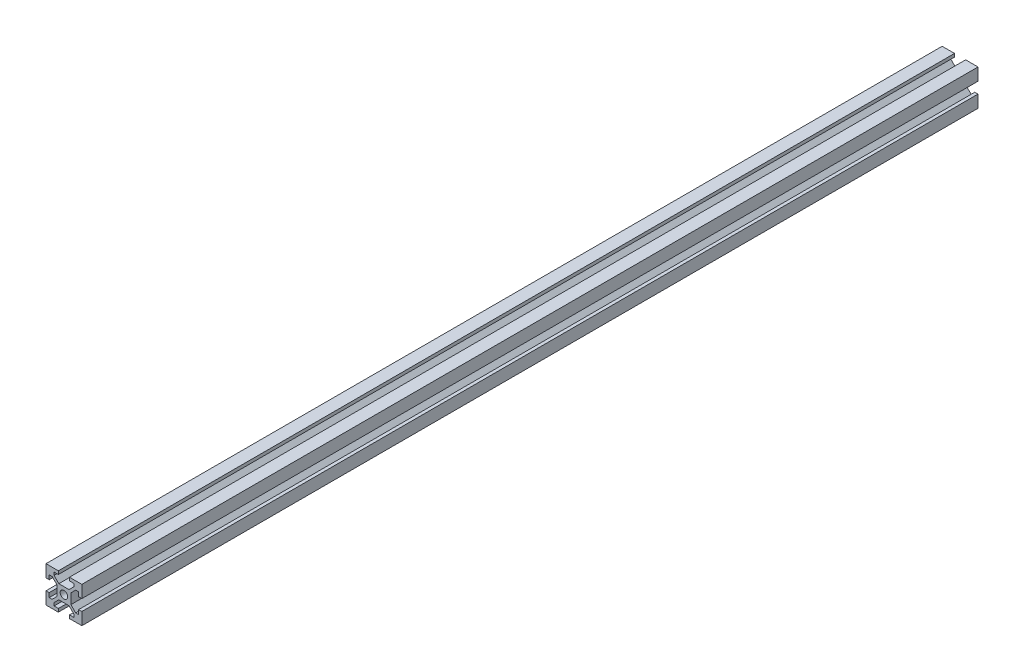
SolidWorks part; units mm, degrees
ref_plane "Front Plane" through (0, 0, 0) normal (0, 0, 1) x (1, 0, 0)
ref_plane "Top Plane" through (0, 0, 0) normal (0, 1, 0) x (1, 0, 0)
ref_plane "Right Plane" through (0, 0, 0) normal (1, 0, 0) x (0, 0, -1)
sketch "Sketch1" plane through (0, 0, 0) normal (0, 0, 1) x (1, 0, 0)
  line L0 (-3.1, 10) -> (-3.1, 8.2007)
  line L1 (-10, 10) -> (-3.1, 10)
  line L2 (-10, 10) -> (-10, 3.1)
  line L3 (-10, -10) -> (-3.1, -10)
  line L4 (10, 10) -> (10, 3.1)
  line L5 (-10, 10) -> (10, -10) construction
  line L6 (-10, -10) -> (10, 10) construction
  line L7 (-3.1, 8.2007) -> (-5.5, 8.2007)
  line L8 (-5.5, 8.2007) -> (-5.5, 6.5607)
  line L9 (-5.5, 6.5607) -> (-2.84, 3.9007)
  line L10 (-2.84, 3.9007) -> (2.84, 3.9007)
  line L11 (2.84, 3.9007) -> (5.5, 6.5607)
  line L12 (5.5, 6.5607) -> (5.5, 8.2007)
  line L13 (5.5, 8.2007) -> (3.1, 8.2007)
  line L14 (3.1, 8.2007) -> (3.1, 10)
  line L15 (-3.1, 8.2007) -> (3.1, 8.2007) construction
  line L16 (-5.5, 6.5607) -> (5.5, 6.5607) construction
  line L17 (3.1, 10) -> (10, 10)
  line L18 (8.2007, 3.1) -> (8.2007, 5.5)
  line L19 (8.2007, 5.5) -> (6.5607, 5.5)
  line L20 (6.5607, 5.5) -> (3.9007, 2.84)
  line L21 (3.9007, 2.84) -> (3.9007, -2.84)
  line L22 (3.9007, -2.84) -> (6.5607, -5.5)
  line L23 (6.5607, -5.5) -> (8.2007, -5.5)
  line L24 (8.2007, -5.5) -> (8.2007, -3.1)
  line L25 (8.2007, 3.1) -> (8.2007, -3.1) construction
  line L26 (6.5607, 5.5) -> (6.5607, -5.5) construction
  line L27 (10, 3.1) -> (8.2007, 3.1)
  line L28 (8.2007, -3.1) -> (10, -3.1)
  line L29 (3.1, -8.2007) -> (5.5, -8.2007)
  line L30 (5.5, -8.2007) -> (5.5, -6.5607)
  line L31 (5.5, -6.5607) -> (2.84, -3.9007)
  line L32 (2.84, -3.9007) -> (-2.84, -3.9007)
  line L33 (-2.84, -3.9007) -> (-5.5, -6.5607)
  line L34 (-5.5, -6.5607) -> (-5.5, -8.2007)
  line L35 (-5.5, -8.2007) -> (-3.1, -8.2007)
  line L36 (3.1, -8.2007) -> (-3.1, -8.2007) construction
  line L37 (5.5, -6.5607) -> (-5.5, -6.5607) construction
  line L38 (3.1, -10) -> (3.1, -8.2007)
  line L39 (-3.1, -8.2007) -> (-3.1, -10)
  line L40 (-8.2007, -3.1) -> (-8.2007, -5.5)
  line L41 (-8.2007, -5.5) -> (-6.5607, -5.5)
  line L42 (-6.5607, -5.5) -> (-3.9007, -2.84)
  line L43 (-3.9007, -2.84) -> (-3.9007, 2.84)
  line L44 (-3.9007, 2.84) -> (-6.5607, 5.5)
  line L45 (-6.5607, 5.5) -> (-8.2007, 5.5)
  line L46 (-8.2007, 5.5) -> (-8.2007, 3.1)
  line L47 (-8.2007, -3.1) -> (-8.2007, 3.1) construction
  line L48 (-6.5607, -5.5) -> (-6.5607, 5.5) construction
  line L49 (-10, -3.1) -> (-8.2007, -3.1)
  line L50 (-8.2007, 3.1) -> (-10, 3.1)
  line L51 (10, -3.1) -> (10, -10)
  line L52 (3.1, -10) -> (10, -10)
  line L53 (-10, -3.1) -> (-10, -10)
  point P0 (0, 0)
  point P8 (0, 8.2007)
  point P18 (0, 3.9007)
  dimension "D1" = 20
  dimension "D2" = 20
  dimension "D3" = 5.68
  dimension "D4" = 6.2
  dimension "D5" = 4.3
  dimension "D6" = 11
  dimension "D7" = 0.75
  dimension "D8" = 4
extrude "Boss-Extrude1" add sketch "Sketch1" along normal blind 500
sketch "Sketch2" plane through (0, 0, 500) normal (0, 0, 1) x (1, 0, 0)
  circle A0 centre (0, 0) radius 2.1
  dimension "D1" = 4.2
extrude "Cut-Extrude1" cut sketch "Sketch2" against normal through all
sketch "Sketch3" plane through (0, 3.9007, 0) normal (0, 1, 0) x (1, 0, 0)
  line L0 (0, 0) -> (0, -500) construction
  line L1 (2.84, -500) -> (-2.84, -500) construction
  circle A0 centre (0, -250) radius 2.1
  dimension "D1" = 4.2
extrude "Cut-Extrude2" cut sketch "Sketch3" against normal through all
